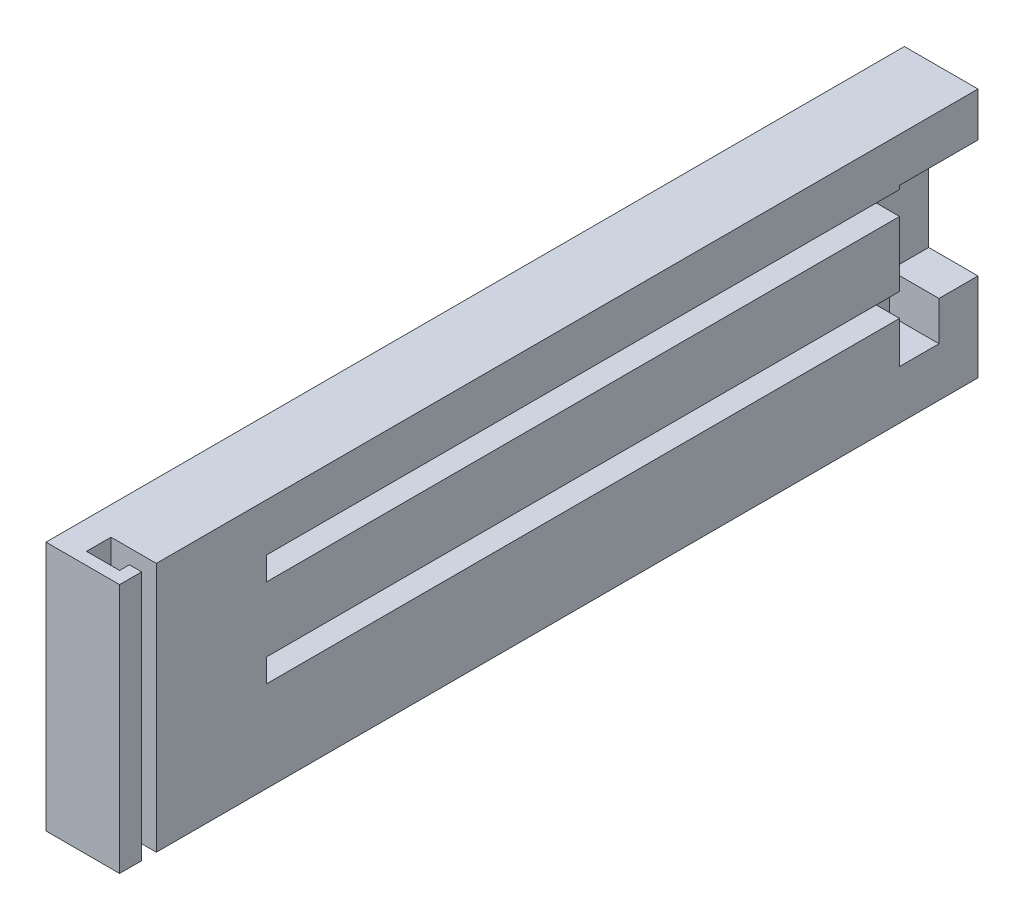
SolidWorks part; units mm, degrees
ref_plane "Front Plane" through (0, 0, 0) normal (0, 0, 1) x (1, 0, 0)
ref_plane "Top Plane" through (0, 0, 0) normal (0, 1, 0) x (1, 0, 0)
ref_plane "Right Plane" through (0, 0, 0) normal (1, 0, 0) x (0, 0, -1)
sketch "Sketch1" plane through (0, 0, 0) normal (1, 0, 0) x (0, 0, -1)
  line L1 (-64.5621, 30.5573) -> (110.4379, 30.5573)
  line L2 (-64.5621, 30.5573) -> (-64.5621, -20.4427)
  line L3 (-64.5621, -20.4427) -> (110.4379, -20.4427)
  line L4 (110.4379, 30.5573) -> (110.4379, -20.4427)
  dimension "D1" = 175
  dimension "D2" = 51
extrude "Boss-Extrude1" add sketch "Sketch1" along normal blind 15 contours L2 L3 L4 L1
sketch "Sketch6" plane through (0, 30.5573, 0) normal (0, 1, 0) x (1, 0, 0)
  line L0 (15, -64.5621) -> (15, -60.0621)
  line L1 (15, -64.5621) -> (15, 110.4379) construction
  line L2 (15, -60.0621) -> (15, -57.0621)
  line L3 (15, -57.0621) -> (12.5, -57.0621)
  line L4 (12.5, -57.0621) -> (5.75, -57.0621)
  line L5 (5.75, -57.0621) -> (5.75, -62.0621)
  line L6 (5.75, -62.0621) -> (12.5, -62.0621)
  line L7 (12.5, -62.0621) -> (12.5, -60.0621)
  line L8 (12.5, -60.0621) -> (15, -60.0621)
  line M11 (15, -64.5621) -> (15, 110.4379)
  dimension "D1" = 4.5
  dimension "D2" = 3
  dimension "D3" = 2.5
  dimension "D4" = 6.75
  dimension "D5" = 5
extrude "Cut-Extrude3" cut sketch "Sketch6" against normal through all contours L7 L8 L3 L4 L5 L6 M11
sketch "Sketch7" plane through (0, 0, -110.4379) normal (0, 0, -1) x (-1, 0, 0)
  line L0 (-15, -20.4427) -> (-15, -1.9427)
  line L1 (-15, 2.8073) -> (-15, 16.0573)
  line L2 (-10.25, 2.8073) -> (-15, 2.8073)
  line L3 (-10.25, 2.8073) -> (-10.25, -1.9427)
  line L4 (-10.25, -1.9427) -> (-15, -1.9427)
  line L5 (-15, 2.8073) -> (-15, -1.9427)
  line L6 (-15, 30.5573) -> (-15, -20.4427) construction
  line L8 (-15, 16.0573) -> (-10.25, 16.0573)
  line L9 (-15, 16.0573) -> (-15, 20.8073)
  line L10 (-15, 20.8073) -> (-10.25, 20.8073)
  line L11 (-10.25, 16.0573) -> (-10.25, 20.8073)
  line M6 (-15, 30.5573) -> (-15, -20.4427)
  dimension "D1" = 18.5
  dimension "D2" = 4.75
  dimension "D3" = 4.75
  dimension "D4" = 13.25
  dimension "D5" = 4.75
  dimension "D6" = 4.75
extrude "Cut-Extrude5" cut sketch "Sketch7" against normal blind 145 contours L4 L3 L2 M6 | L9 L8 L11 L10
sketch "Sketch8" plane through (0, 0, -110.4379) normal (0, 0, -1) x (-1, 0, 0)
  line L0 (-15, 30.5573) -> (-15, 20.8073) construction
  line L1 (-15, 21.5573) -> (-4.95, 21.5573)
  line L2 (-15, 21.5573) -> (-15, -2.4427)
  line L3 (-15, -2.4427) -> (-4.95, -2.4427)
  line L4 (-4.95, 21.5573) -> (-4.95, -2.4427)
  line L5 (-15, -20.4427) -> (-15, -2.4427)
  point P9 (0, 0)
  line M6 (-10.25, 2.8073) -> (-10.25, -1.9427)
  line M7 (-10.25, -1.9427) -> (-15, -1.9427)
  line M8 (-15, -1.9427) -> (-15, -20.4427)
  line M12 (-15, 30.5573) -> (-15, 20.8073)
  line M13 (-15, 2.8073) -> (-10.25, 2.8073)
  dimension "D1" = 24
  dimension "D2" = 18
  dimension "D3" = 10.05
extrude "Cut-Extrude6" cut sketch "Sketch8" against normal blind 16 contours L4 L1 L3 M12 M13 M6 M7 M8
sketch "Sketch9" plane through (0, -2.4427, 0) normal (0, 1, 0) x (1, 0, 0)
  line L0 (4.95, 94.4379) -> (4.95, 110.4379) construction
  line L1 (15, 94.4379) -> (4.95, 94.4379)
  line L2 (15, 94.4379) -> (15, 102.4879)
  line L3 (15, 102.4879) -> (4.95, 102.4879)
  line L4 (4.95, 94.4379) -> (4.95, 102.4879)
  dimension "D1" = 8.05
extrude "Cut-Extrude7" cut sketch "Sketch9" against normal blind 8
